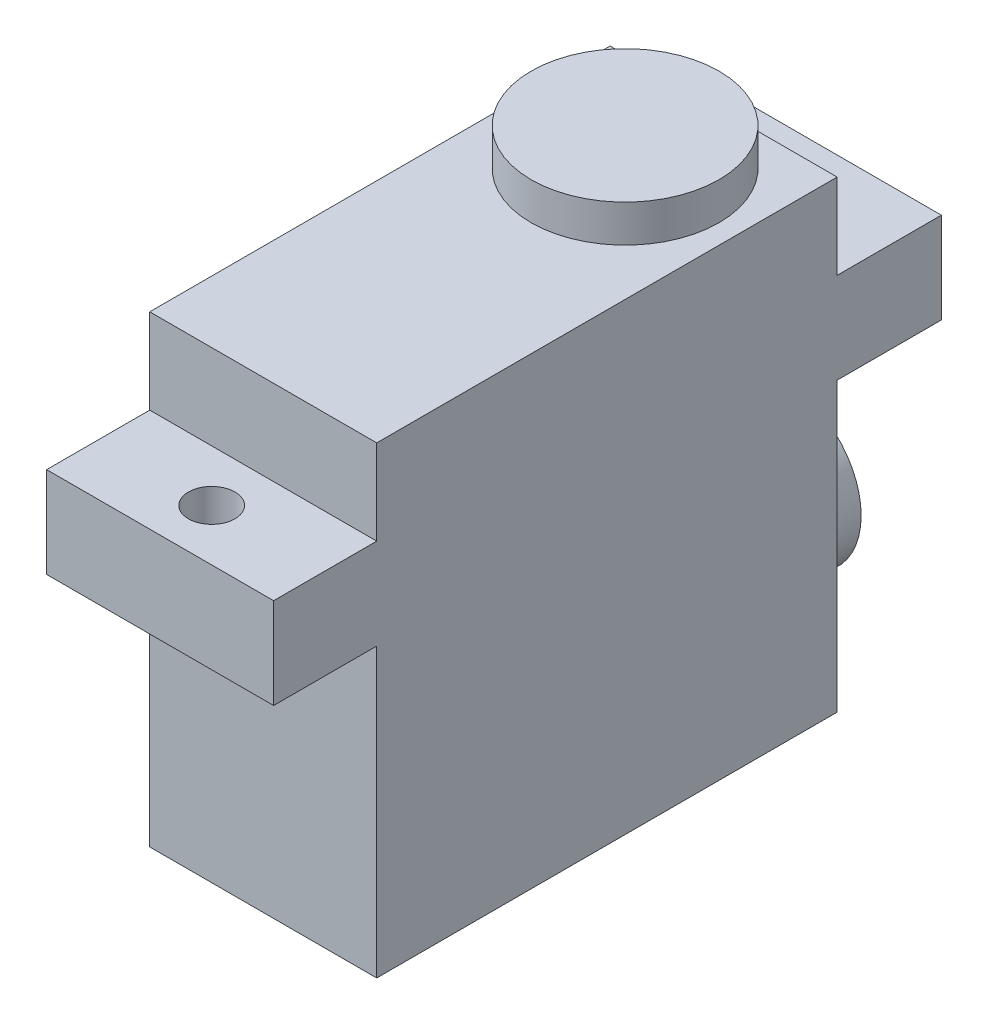
SolidWorks part; units mm, degrees
ref_plane "Front Plane" through (0, 0, 0) normal (0, 0, 1) x (1, 0, 0)
ref_plane "Top Plane" through (0, 0, 0) normal (0, 1, 0) x (1, 0, 0)
ref_plane "Right Plane" through (0, 0, 0) normal (1, 0, 0) x (0, 0, -1)
sketch "Sketch1" plane through (0, 0, 0) normal (0, 1, 0) x (1, 0, 0)
  line L1 (0, 0) -> (15.24, 0)
  line L2 (0, 0) -> (0, 30.9118)
  line L3 (0, 30.9118) -> (15.24, 30.9118)
  line L4 (15.24, 0) -> (15.24, 30.9118)
  dimension "D1" = 15.24
  dimension "D2" = 30.9118
extrude "Boss-Extrude1" add sketch "Sketch1" along normal blind 31.115
sketch "Sketch2" plane through (0, 0, 0) normal (0, 0, 1) x (1, 0, 0)
  line L0 (0, 31.115) -> (0, 0) construction
  line L1 (0, 25.4) -> (15.24, 25.4)
  line L2 (0, 25.4) -> (0, 19.304)
  line L3 (0, 19.304) -> (15.24, 19.304)
  line L4 (15.24, 25.4) -> (15.24, 19.304)
  line L5 (15.24, 31.115) -> (15.24, 0) construction
  line L6 (0, 0) -> (15.24, 0) construction
  dimension "D1" = 19.304
  dimension "D2" = 6.096
extrude "Boss-Extrude2" add sketch "Sketch2" along normal blind 6.9215 and the other way blind 37.9095
sketch "Sketch3" plane through (0, 0, -30.9118) normal (0, 0, -1) x (-1, 0, 0)
  line L0 (-15.24, 0) -> (0, 0) construction
  circle A0 centre (-7.62, 8.2804) radius 5.2705
  dimension "D1" = 10.541
  dimension "D2" = 8.2804
extrude "Boss-Extrude3" add sketch "Sketch3" along normal blind 3.9624
sketch "Sketch4" plane through (0, 31.115, 0) normal (0, 1, 0) x (1, 0, 0)
  line L0 (15.24, 30.9118) -> (0, 30.9118) construction
  circle A0 centre (7.62, 24.2951) radius 6.3119
  dimension "D1" = 12.6238
  dimension "D2" = 6.6167
extrude "Boss-Extrude4" add sketch "Sketch4" along normal blind 2.5019
sketch "Sketch8" plane through (0, 25.4, 0) normal (0, 1, 0) x (1, 0, 0)
  circle A0 centre (7.62, -3.4608) radius 1.5621
  dimension "D1" = 3.1242
extrude "Cut-Extrude1" cut sketch "Sketch8" against normal up to next
sketch "Sketch9" plane through (0, 25.4, 0) normal (0, 1, 0) x (1, 0, 0)
  circle A0 centre (7.62, 34.4107) radius 1.5621
  dimension "D1" = 3.1242
extrude "Cut-Extrude2" cut sketch "Sketch9" against normal up to next
